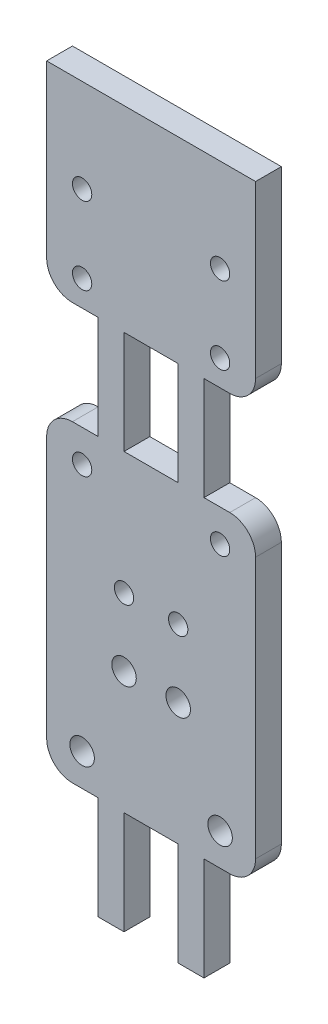
SolidWorks part; units mm, degrees
ref_plane "Front Plane" through (0, 0, 0) normal (0, 0, 1) x (1, 0, 0)
ref_plane "Top Plane" through (0, 0, 0) normal (0, 1, 0) x (1, 0, 0)
ref_plane "Right Plane" through (0, 0, 0) normal (1, 0, 0) x (0, 0, -1)
sketch "Sketch1" plane through (0, 0, 0) normal (0, 0, 1) x (1, 0, 0)
  line L0 (4, 44.7) -> (4, 52.7)
  line L1 (0, -0.06) -> (16.2, -0.06) construction
  line L2 (8.1, -0.06) -> (8.1, 67.93) construction
  line L3 (6, 12.44) -> (10.2, 12.44) construction
  line L4 (6, 20.44) -> (10.2, 20.44)
  line L5 (6, 44.7) -> (6, 52.7)
  line L6 (0, 54.7) -> (0, 67.93)
  line L7 (6, 44.7) -> (10.2, 44.7)
  line L8 (6, 52.7) -> (10.2, 52.7)
  line L9 (2, 44.7) -> (4, 44.7)
  line L10 (0, 67.93) -> (16.2, 67.93)
  line L11 (2, 20.44) -> (4, 20.44)
  line L12 (0, 22.44) -> (0, 42.7)
  line L13 (16.2, 12.44) -> (12.2, 12.44) construction
  line L14 (12.2, 20.44) -> (12.2, 12.44)
  line L15 (10.2, 12.44) -> (10.2, 20.44)
  line L16 (16.2, 12.44) -> (16.2, -0.06) construction
  line L17 (14.2, 52.7) -> (12.2, 52.7)
  line L18 (16.2, 22.44) -> (16.2, 42.7)
  line L19 (14.2, 20.44) -> (12.2, 20.44)
  line L20 (14.2, 44.7) -> (12.2, 44.7)
  line L21 (16.2, 54.7) -> (16.2, 67.93)
  line L22 (10.2, 44.7) -> (10.2, 52.7)
  line L23 (12.2, 44.7) -> (12.2, 52.7)
  line L24 (4, 12.44) -> (6, 12.44)
  line L25 (10.2, 12.44) -> (12.2, 12.44)
  line L36 (2, 52.7) -> (4, 52.7)
  line L46 (0, 12.44) -> (0, -0.06) construction
  line L47 (6, 12.44) -> (6, 20.44)
  line L48 (4, 20.44) -> (4, 12.44)
  line L49 (0, 12.44) -> (4, 12.44) construction
  circle A0 centre (2.75, 60.7) radius 0.75
  circle A1 centre (13.35, 9.94) radius 0.95 construction
  circle A2 centre (13.35, 3.94) radius 0.95 construction
  circle A3 centre (13.45, 54.7) radius 0.75
  arc A4 (16.2, 54.7) -> (14.2, 52.7) centre (14.2, 54.7) cw
  circle A5 centre (13.45, 42.2) radius 0.75
  circle A6 centre (13.45, 22.94) radius 0.95
  circle A7 centre (10.2, 29.94) radius 0.95
  arc A8 (16.2, 22.44) -> (14.2, 20.44) centre (14.2, 22.44) cw
  circle A9 centre (6, 35.2) radius 0.75
  arc A10 (14.2, 44.7) -> (16.2, 42.7) centre (14.2, 42.7) cw
  circle A11 centre (13.45, 60.7) radius 0.75
  circle A12 centre (10.2, 35.2) radius 0.75
  arc A27 (2, 44.7) -> (0, 42.7) centre (2, 42.7) ccw
  arc A31 (0, 22.44) -> (2, 20.44) centre (2, 22.44) ccw
  circle A33 centre (6, 29.94) radius 0.95
  circle A35 centre (2.75, 22.94) radius 0.95
  circle A37 centre (2.75, 42.2) radius 0.75
  arc A43 (0, 54.7) -> (2, 52.7) centre (2, 54.7) ccw
  circle A45 centre (2.75, 54.7) radius 0.75
  circle A46 centre (2.85, 3.94) radius 0.95 construction
  circle A47 centre (2.85, 9.94) radius 0.95 construction
  point P30 (8.1, 20.44)
  point P31 (8.1, 12.44)
  point P47 (8.1, 52.7)
  point P48 (8.1, 44.7)
  dimension "D10" = 1.9
  dimension "D11" = 2
  dimension "D18" = 2
  dimension "D26" = 2
  dimension "D28" = 6
  dimension "D1" = 8
  dimension "D2" = 8
  dimension "D3" = 4
  dimension "D4" = 6
  dimension "D5" = 2.5
  dimension "D6" = 4
  dimension "D7" = 2.85
  dimension "D8" = 2.85
  dimension "D9" = 2
  dimension "D12" = 2.5
  dimension "D13" = 2.75
  dimension "D14" = 9.5
  dimension "D15" = 6
  dimension "D16" = 2
  dimension "D17" = 2
  dimension "D19" = 2.5
  dimension "D20" = 2.75
  dimension "D21" = 2
  dimension "D22" = 2
  dimension "D23" = 2.75
  dimension "D24" = 24.26
  dimension "D25" = 9.5
  dimension "D27" = 2
  dimension "D29" = 2
  dimension "D30" = 2.75
  dimension "D31" = 8.1
  dimension "D32" = 15.23
  dimension "D33" = 6
extrude "Boss-Extrude1" add sketch "Sketch1" along normal blind 2
sketch "Sketch2" plane through (0, 0, 2) normal (0, 0, 1) x (1, 0, 0)
  line L0 (12.2, 12.44) -> (4, 12.44)
  line L1 (4, 20.44) -> (12.2, 20.44)
  line L2 (12.2, 20.44) -> (12.2, 12.44)
  line L3 (4, 12.44) -> (4, 20.44)
  line L4 (4, 52.7) -> (12.2, 52.7)
  line L5 (12.2, 52.7) -> (12.2, 44.7)
  line L6 (12.2, 44.7) -> (4, 44.7)
  line L7 (4, 44.7) -> (4, 52.7)
extrude "Cut-Extrude1" [suppressed] cut sketch "Sketch2" against normal up to surface (2 mm away)
equation "\"D24@Sketch1\"= \"HL@parametersSketch@prostheticParameters.SLDPRT\" * 0.196 - 4 - 8'Thumb PIP Length"
equation "\"D32@Sketch1\" = \"HL@parametersSketch@prostheticParameters.SLDPRT\" * 0.158 - 4 - 10'Thumb DIP Length - Gap Fingertip"
equation "\"D31@Sketch1\"= \"fingerWidth@parametersSketch@prostheticParameters.SLDPRT\" / 2'Finger Width"
equation "\"D10@Sketch1\"= 1.5 + \"tol1@parametersSketch@prostheticParameters.SLDPRT\""
